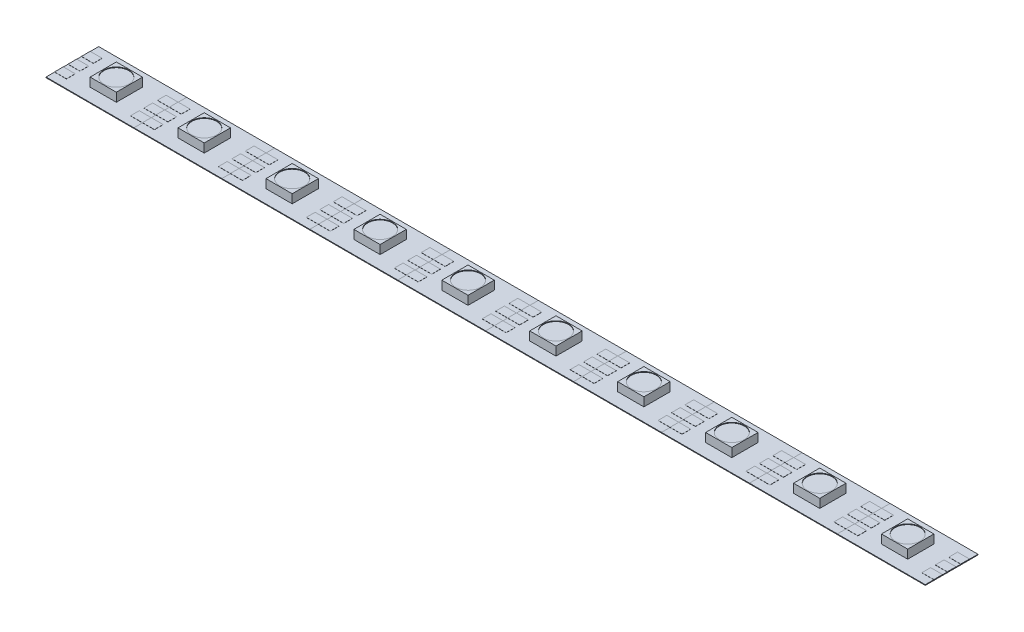
SolidWorks part; units mm, degrees
ref_plane "Front Plane" through (0, 0, 0) normal (0, 0, 1) x (1, 0, 0)
ref_plane "Top Plane" through (0, 0, 0) normal (0, 1, 0) x (1, 0, 0)
ref_plane "Right Plane" through (0, 0, 0) normal (1, 0, 0) x (0, 0, -1)
sketch "Sketch1" plane through (0, 0, 0) normal (0, 1, 0) x (1, 0, 0)
  line L0 (-8.3058, 4.9784) -> (8.3058, -4.9784) construction
  line L1 (-8.3058, 4.9784) -> (8.3058, 4.9784)
  line L2 (-8.3058, 4.9784) -> (-8.3058, -4.9784)
  line L3 (-8.3058, -4.9784) -> (8.3058, -4.9784)
  line L4 (8.3058, 4.9784) -> (8.3058, -4.9784)
  dimension "D1" = 9.9568
  dimension "D2" = 16.6116
extrude "Boss-Extrude1" add sketch "Sketch1" along normal blind 0.127
sketch "Sketch3" plane through (0, 0.127, 0) normal (0, 1, 0) x (1, 0, 0)
  line L0 (-8.3058, 4.9784) -> (8.3058, -4.9784) construction
  line L1 (-2.4765, 2.4765) -> (2.4765, -2.4765) construction
  line L2 (-2.4765, 2.4765) -> (2.4765, 2.4765)
  line L3 (-2.4765, 2.4765) -> (-2.4765, -2.4765)
  line L4 (-2.4765, -2.4765) -> (2.4765, -2.4765)
  line L5 (2.4765, 2.4765) -> (2.4765, -2.4765)
  dimension "D1" = 4.953
extrude "Boss-Extrude3" add sketch "Sketch3" along normal blind 1.651
sketch "Sketch4" plane through (0, 0.127, 0) normal (0, 1, 0) x (1, 0, 0)
  line L0 (-8.3058, 0) -> (8.3058, 0) construction
  line L1 (-8.3058, 4.9784) -> (-8.3058, -4.9784) construction
  line L2 (8.3058, -4.9784) -> (8.3058, 4.9784) construction
  line L3 (-6.047, 0) -> (-8.3058, 0) construction
  line L4 (-8.3058, 0.8255) -> (-6.047, 0.8255)
  line L5 (-8.3058, 0.8255) -> (-8.3058, -0.8255)
  line L6 (-8.3058, -0.8255) -> (-6.047, -0.8255)
  line L7 (-6.047, 0.8255) -> (-6.047, -0.8255)
  line L8 (-8.3058, 3.3655) -> (-6.047, 3.3655)
  line L9 (-6.047, 3.3655) -> (-6.047, 1.7145)
  line L10 (-8.3058, 1.7145) -> (-6.047, 1.7145)
  line L11 (-8.3058, 3.3655) -> (-8.3058, 1.7145)
  line L12 (-6.047, -3.3655) -> (-6.047, -1.7145)
  line L13 (-8.3058, -1.7145) -> (-6.047, -1.7145)
  line L14 (-8.3058, -3.3655) -> (-8.3058, -1.7145)
  line L15 (-8.3058, -3.3655) -> (-6.047, -3.3655)
  line L16 (0, 0) -> (0, -4.9784) construction
  line L17 (-8.3058, -4.9784) -> (8.3058, -4.9784) construction
  line L18 (8.3058, -3.3655) -> (8.3058, -1.7145)
  line L19 (8.3058, -3.3655) -> (6.047, -3.3655)
  line L20 (6.047, -3.3655) -> (6.047, -1.7145)
  line L21 (8.3058, -1.7145) -> (6.047, -1.7145)
  line L22 (8.3058, 0.8255) -> (8.3058, -0.8255)
  line L23 (8.3058, -0.8255) -> (6.047, -0.8255)
  line L24 (6.047, 0.8255) -> (6.047, -0.8255)
  line L25 (8.3058, 0.8255) -> (6.047, 0.8255)
  line L26 (8.3058, 1.7145) -> (6.047, 1.7145)
  line L27 (6.047, 3.3655) -> (6.047, 1.7145)
  line L28 (8.3058, 3.3655) -> (8.3058, 1.7145)
  line L29 (8.3058, 3.3655) -> (6.047, 3.3655)
  dimension "D1" = 1.651
  dimension "D2" = 2
extrude "Boss-Extrude4" add sketch "Sketch4" along normal blind 0.0254
sketch "Sketch5" plane through (0, 1.778, 0) normal (0, 1, 0) x (1, 0, 0)
  circle A0 centre (0, 0) radius 2.3483
extrude "Cut-Extrude1" cut sketch "Sketch5" against normal blind 0.127
pattern_linear "LPattern1" count 10 spacing 16.6116 along (1, 0, 0) of "Boss-Extrude3", "Boss-Extrude4", "Cut-Extrude1", "Boss-Extrude1"
